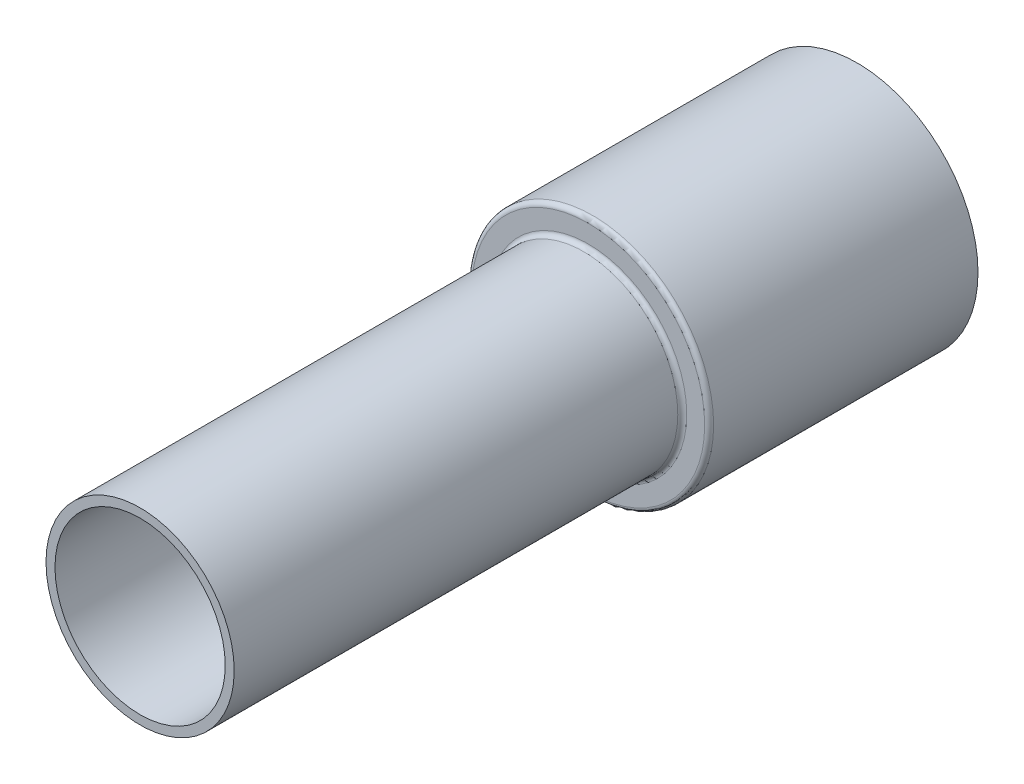
SolidWorks part; units mm, degrees
material "PVC Rigid"
ref_plane "Front Plane" through (0, 0, 0) normal (0, 0, 1) x (1, 0, 0)
ref_plane "Top Plane" through (0, 0, 0) normal (0, 1, 0) x (1, 0, 0)
ref_plane "Right Plane" through (0, 0, 0) normal (1, 0, 0) x (0, 0, -1)
sketch "Sketch1" plane through (0, 0, 0) normal (1, 0, 0) x (0, 0, -1)
  line L0 (0, 0) -> (80, 0)
  line L1 (0, 9.5) -> (50.5, 9.5)
  line L2 (51.5, 12.5) -> (80, 12.5)
  line L3 (0, 10.5) -> (49.5, 10.5)
  line L4 (50.5, 13.5) -> (80, 13.5)
  line L5 (80, 13.5) -> (80, 12.5)
  line L6 (50, 13) -> (50, 11)
  line L7 (51, 12) -> (51, 10)
  line L8 (50, 13.5) -> (50, 8) construction
  line L9 (0, 10.5) -> (0, 9.5)
  line L10 (0, 13.5) -> (80, 13.5) construction
  line L11 (0, 12.5) -> (80, 12.5) construction
  line L12 (0, 9.5) -> (80, 9.5) construction
  line L13 (0, 10.5) -> (80, 10.5) construction
  line L14 (51, 13.5) -> (51, 8) construction
  arc A0 (50, 13) -> (50.5, 13.5) centre (50.5, 13) cw
  arc A1 (51, 12) -> (51.5, 12.5) centre (51.5, 12) cw
  arc A2 (50.5, 9.5) -> (51, 10) centre (50.5, 10) ccw
  arc A3 (50, 11) -> (49.5, 10.5) centre (49.5, 11) cw
  point P11 (50, 13.5)
  point P21 (50, 13.5)
  dimension "D8" = 0.5
  dimension "D1" = 80
  dimension "D6" = 30
  dimension "D2" = 9.5
  dimension "D3" = 12.5
  dimension "D4" = 10.5
  dimension "D5" = 13.5
  dimension "D7" = 1
revolve "Revolve4" add sketch "Sketch1" angle 360 about L0
